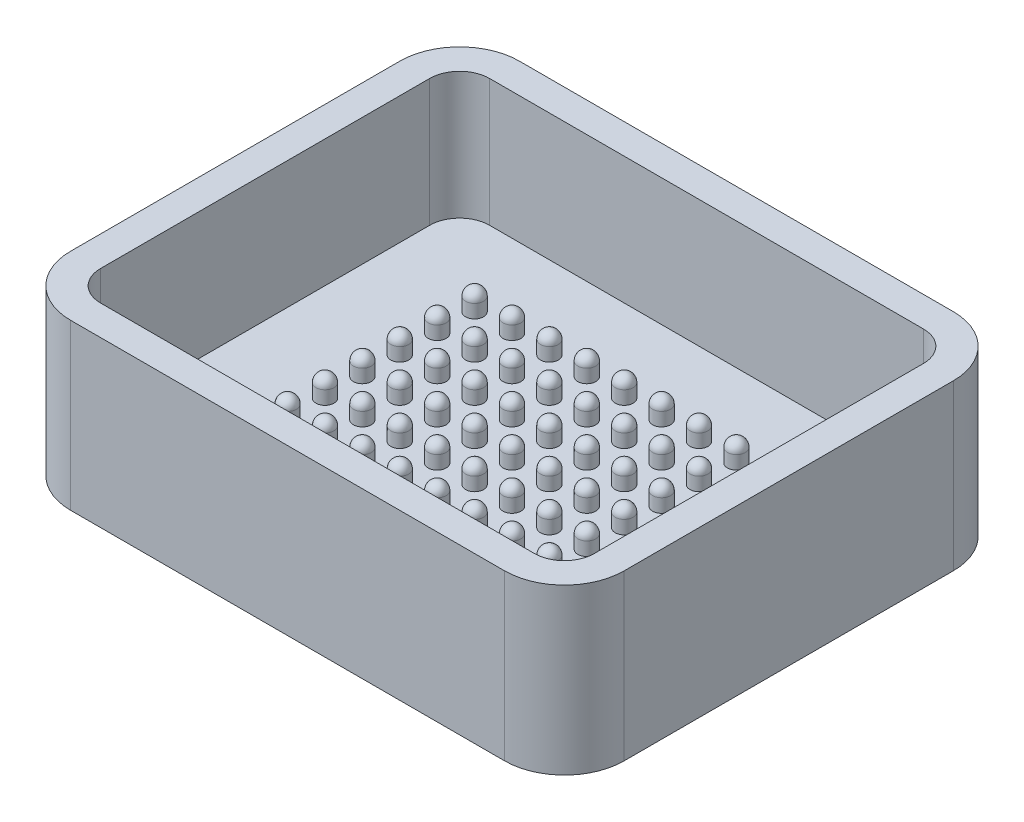
SolidWorks part; units mm, degrees
other "相机1"
ref_plane "前视基准面" through (0, 0, 0) normal (0, 0, 1) x (1, 0, 0)
ref_plane "上视基准面" through (0, 0, 0) normal (0, 1, 0) x (1, 0, 0)
ref_plane "右视基准面" through (0, 0, 0) normal (1, 0, 0) x (0, 0, -1)
other "Configuration Table"
sketch "草图1" plane through (0, 0, 0) normal (0, 1, 0) x (1, 0, 0)
  line L1 (-16.5, 13) -> (16.5, 13)
  line L2 (-16.5, 13) -> (-16.5, -13)
  line L3 (-16.5, -13) -> (16.5, -13)
  line L4 (16.5, 13) -> (16.5, -13)
  line L5 (-16.5, 13) -> (16.5, -13) construction
  line L6 (-16.5, -13) -> (16.5, 13) construction
  point P0 (0, 0)
  dimension "D1" = 33
  dimension "D2" = 26
extrude "凸台-拉伸1" add sketch "草图1" along normal blind 2.5
sketch "草图2" plane through (0, 2.5, 0) normal (0, 1, 0) x (1, 0, 0)
  line L0 (0, 13) -> (0, 0) construction
  line L1 (16.5, 13) -> (-16.5, 13) construction
  line L2 (0, 0) -> (16.5, 0) construction
  line L3 (16.5, -13) -> (16.5, 13) construction
  line L4 (0, 2.5) -> (2.5, 2.5) construction
  line L5 (2.5, 2.5) -> (2.5, 0) construction
  circle A0 centre (0, 0) radius 0.6
  circle A1 centre (2.5, 0) radius 0.6
  circle A2 centre (5, 0) radius 0.6
  circle A3 centre (7.5, 0) radius 0.6
  circle A4 centre (10, 0) radius 0.6
  circle A5 centre (2.5, 2.5) radius 0.6
  circle A6 centre (5, 2.5) radius 0.6
  circle A7 centre (7.5, 2.5) radius 0.6
  circle A8 centre (10, 2.5) radius 0.6
  circle A9 centre (2.5, 5) radius 0.6
  circle A10 centre (5, 5) radius 0.6
  circle A11 centre (7.5, 5) radius 0.6
  circle A12 centre (10, 5) radius 0.6
  circle A13 centre (2.5, 7.5) radius 0.6
  circle A14 centre (5, 7.5) radius 0.6
  circle A15 centre (7.5, 7.5) radius 0.6
  circle A16 centre (10, 7.5) radius 0.6
  circle A17 centre (0, 2.5) radius 0.6
  circle A18 centre (0, 5) radius 0.6
  circle A19 centre (0, 7.5) radius 0.6
  circle A20 centre (10, -7.5) radius 0.6
  circle A21 centre (7.5, -7.5) radius 0.6
  circle A22 centre (5, -7.5) radius 0.6
  circle A23 centre (2.5, -7.5) radius 0.6
  circle A24 centre (10, -5) radius 0.6
  circle A25 centre (7.5, -5) radius 0.6
  circle A26 centre (5, -5) radius 0.6
  circle A27 centre (2.5, -5) radius 0.6
  circle A28 centre (10, -2.5) radius 0.6
  circle A29 centre (7.5, -2.5) radius 0.6
  circle A30 centre (5, -2.5) radius 0.6
  circle A31 centre (2.5, -2.5) radius 0.6
  circle A32 centre (-2.5, -2.5) radius 0.6
  circle A33 centre (-5, -2.5) radius 0.6
  circle A34 centre (-7.5, -2.5) radius 0.6
  circle A35 centre (-10, -2.5) radius 0.6
  circle A36 centre (-2.5, -5) radius 0.6
  circle A37 centre (-5, -5) radius 0.6
  circle A38 centre (-7.5, -5) radius 0.6
  circle A39 centre (-10, -5) radius 0.6
  circle A40 centre (-2.5, -7.5) radius 0.6
  circle A41 centre (-5, -7.5) radius 0.6
  circle A42 centre (-7.5, -7.5) radius 0.6
  circle A43 centre (-10, -7.5) radius 0.6
  circle A44 centre (-10, 7.5) radius 0.6
  circle A45 centre (-7.5, 7.5) radius 0.6
  circle A46 centre (-5, 7.5) radius 0.6
  circle A47 centre (-2.5, 7.5) radius 0.6
  circle A48 centre (-10, 5) radius 0.6
  circle A49 centre (-7.5, 5) radius 0.6
  circle A50 centre (-5, 5) radius 0.6
  circle A51 centre (-2.5, 5) radius 0.6
  circle A52 centre (-10, 2.5) radius 0.6
  circle A53 centre (-7.5, 2.5) radius 0.6
  circle A54 centre (-5, 2.5) radius 0.6
  circle A55 centre (-2.5, 2.5) radius 0.6
  circle A56 centre (-10, 0) radius 0.6
  circle A57 centre (-7.5, 0) radius 0.6
  circle A58 centre (-5, 0) radius 0.6
  circle A59 centre (-2.5, 0) radius 0.6
  circle A60 centre (0, -7.5) radius 0.6
  circle A61 centre (0, -5) radius 0.6
  circle A62 centre (0, -2.5) radius 0.6
  dimension "D1" = 1.2
  dimension "D4" = 2.5
  dimension "D2" = 5
  dimension "D3" = 4
extrude "凸台-拉伸2" add sketch "草图2" along normal blind 1.5
fillet "圆角1" radius 0.6 63 edges at (0, 4, 1.9) (0, 4, 4.4) (0, 4, 6.9) (-2.5, 4, -0.6) (-5, 4, -0.6) (-7.5, 4, -0.6) (-10, 4, -0.6) (-2.5, 4, -3.1) (-5, 4, -3.1) (-7.5, 4, -3.1) (-10, 4, -3.1) (-2.5, 4, -5.6) (-5, 4, -5.6) (-7.5, 4, -5.6) (-10, 4, -5.6) (-2.5, 4, -8.1) (-5, 4, -8.1) (-7.5, 4, -8.1) (-10, 4, -8.1) (-10, 4, 8.1) (-7.5, 4, 8.1) (-5, 4, 8.1) (-2.5, 4, 8.1) (-10, 4, 5.6) (-7.5, 4, 5.6) (-5, 4, 5.6) (-2.5, 4, 5.6) (-10, 4, 3.1) (-7.5, 4, 3.1) (-5, 4, 3.1) (-2.5, 4, 3.1) (2.5, 4, 1.9) (5, 4, 1.9) (7.5, 4, 1.9) (10, 4, 1.9) (2.5, 4, 4.4) (5, 4, 4.4) (7.5, 4, 4.4) (10, 4, 4.4) (2.5, 4, 6.9) (5, 4, 6.9) (7.5, 4, 6.9) (10, 4, 6.9) (0, 4, -6.9) (0, 4, -4.4) (0, 4, -1.9) (7.5, 4, -6.9) (5, 4, -6.9) (2.5, 4, -6.9) (7.5, 4, -4.4) (5, 4, -4.4) (2.5, 4, -4.4) (10, 4, -1.9) (7.5, 4, -1.9) (5, 4, -1.9) (2.5, 4, -1.9) (10, 4, 0.6) (7.5, 4, 0.6) (5, 4, 0.6) (2.5, 4, 0.6) (0, 4, 0.6) (10, 4, -4.4) (10, 4, -6.9)
sketch "草图3" plane through (0, 0, 0) normal (0, -1, 0) x (1, 0, 0)
  line L1 (-16.5, 13) -> (16.5, 13)
  line L2 (-16.5, 13) -> (-16.5, -13)
  line L3 (-16.5, -13) -> (16.5, -13)
  line L4 (16.5, 13) -> (16.5, -13)
  line L5 (-16.5, 13) -> (16.5, -13) construction
  line L6 (-16.5, -13) -> (16.5, 13) construction
  line L7 (-18.5, 15) -> (18.5, 15)
  line L8 (-18.5, 15) -> (-18.5, -15)
  line L9 (-18.5, -15) -> (18.5, -15)
  line L10 (18.5, 15) -> (18.5, -15)
  line L11 (-18.5, 15) -> (18.5, -15) construction
  line L12 (-18.5, -15) -> (18.5, 15) construction
  point P0 (0, 0)
  point P7 (0, 0)
  dimension "D1" = 2
  dimension "D2" = 2
extrude "凸台-拉伸3" add sketch "草图3" against normal blind 11
fillet "圆角3" radius 2 4 edges at (-16.5, 6.75, 13) (16.5, 6.75, 13) (16.5, 6.75, -13) (-16.5, 6.75, -13)
fillet "圆角4" radius 4 4 edges at (18.5, 5.5, 15) (-18.5, 5.5, 15) (18.5, 5.5, -15) (-18.5, 5.5, -15)
